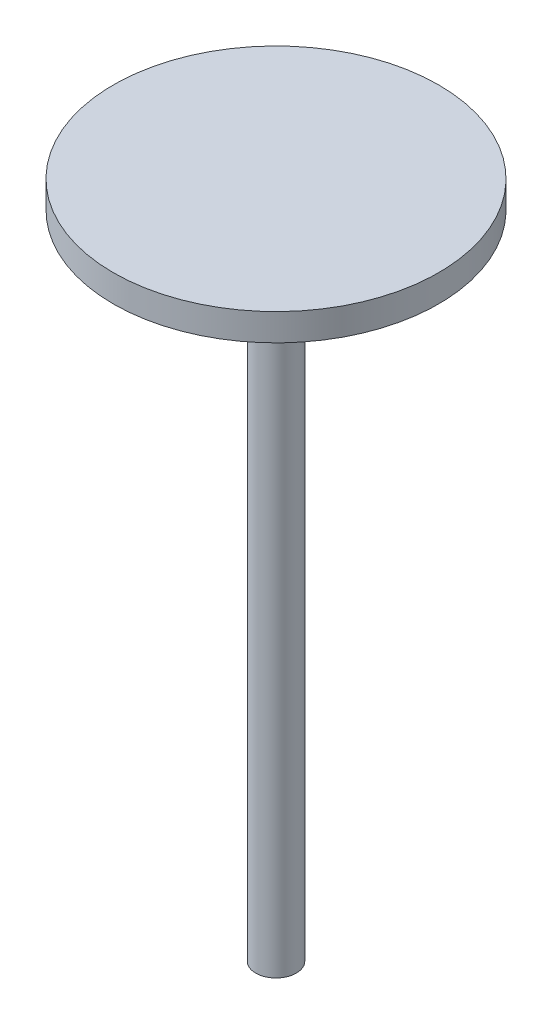
SolidWorks part; units mm, degrees
ref_plane "Front Plane" through (0, 0, 0) normal (0, 0, 1) x (1, 0, 0)
ref_plane "Top Plane" through (0, 0, 0) normal (0, 1, 0) x (1, 0, 0)
ref_plane "Right Plane" through (0, 0, 0) normal (1, 0, 0) x (0, 0, -1)
sketch "Sketch1" plane through (0, 0, 0) normal (0, 1, 0) x (1, 0, 0)
  circle A0 centre (0, 0) radius 9.525
  dimension "D1" = 19.05
extrude "Boss-Extrude1" add sketch "Sketch1" along normal blind 304.8
sketch "Sketch2" plane through (0, 304.8, 0) normal (0, 1, 0) x (1, 0, 0)
  circle A0 centre (0, 0) radius 28.2575
  dimension "D1" = 56.515
extrude "Boss-Extrude2" add sketch "Sketch2" along normal blind 6.35
sketch "Sketch3" plane through (0, 311.15, 0) normal (0, 1, 0) x (1, 0, 0)
  circle A0 centre (0, 0) radius 76.2
  dimension "D1" = 152.4
extrude "Boss-Extrude3" add sketch "Sketch3" along normal blind 6.35
sketch "Sketch5" plane through (0, 311.15, 0) normal (0, -1, 0) x (1, 0, 0)
  circle A0 centre (0, 0) radius 76.2
  circle A1 centre (0, 0) radius 70.1675
  point P4 (0, 0)
  dimension "D1" = 140.335
extrude "Boss-Extrude4" add sketch "Sketch5" along normal blind 6.35
